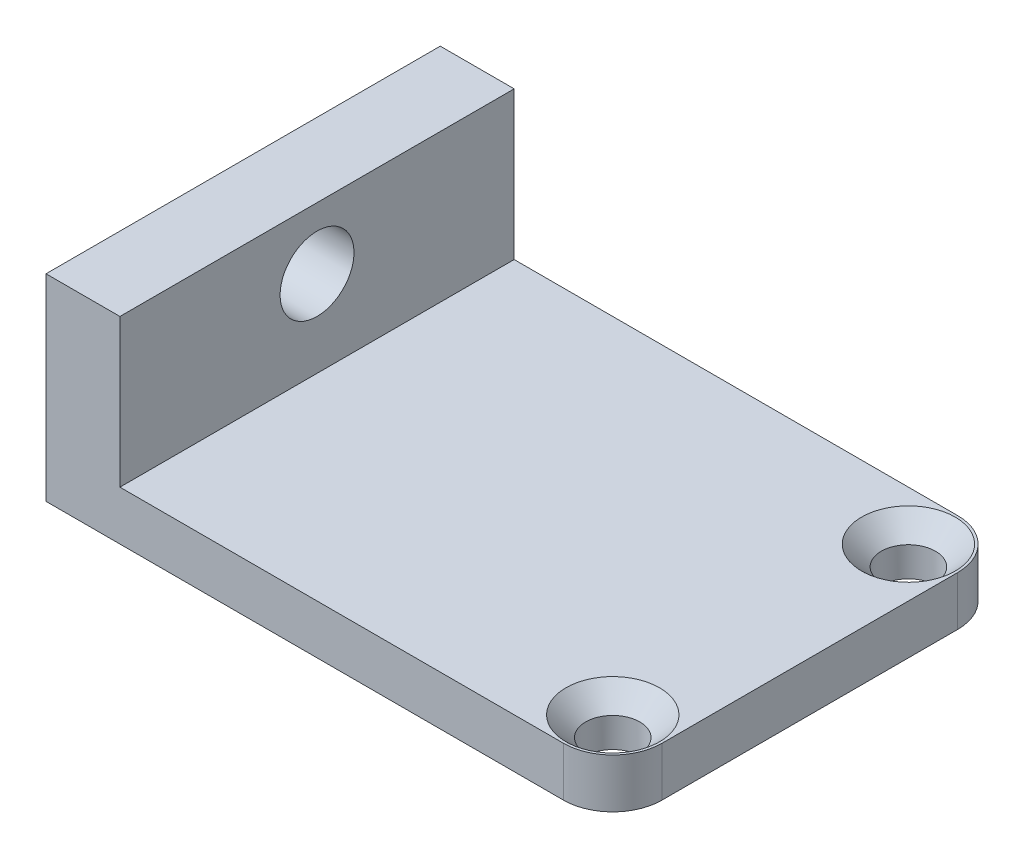
SolidWorks part; units mm, degrees
ref_plane "Front Plane" through (0, 0, 0) normal (0, 0, 1) x (1, 0, 0)
ref_plane "Top Plane" through (0, 0, 0) normal (0, 1, 0) x (1, 0, 0)
ref_plane "Right Plane" through (0, 0, 0) normal (1, 0, 0) x (0, 0, -1)
sketch "Sketch1" plane through (0, 0, 0) normal (0, 0, 1) x (1, 0, 0)
  line L0 (0, 0) -> (0, 8)
  line L1 (0, 8) -> (3, 8)
  line L2 (3, 8) -> (3, 2)
  line L3 (3, 2) -> (23, 2)
  line L4 (23, 2) -> (23, 0)
  line L5 (23, 0) -> (0, 0)
  dimension "D1" = 20
  dimension "D2" = 2
  dimension "D3" = 3
  dimension "D4" = 8
extrude "Boss-Extrude1" add sketch "Sketch1" along normal blind 16
sketch "Sketch2" plane through (0, 2, 0) normal (0, 1, 0) x (1, 0, 0)
  line L0 (23, 0) -> (3, 0) construction
  line L1 (3, -16) -> (3, 0) construction
  circle A0 centre (21, -2) radius 1.1
  circle A1 centre (21, -14) radius 1.1
  dimension "D1" = 2.2
  dimension "D2" = 2.2
  dimension "D3" = 2
  dimension "D4" = 12
  dimension "D5" = 18
  dimension "D6" = 18
extrude "Cut-Extrude1" cut sketch "Sketch2" against normal blind 2
sketch "Sketch3" plane through (0, 0, 0) normal (-1, 0, 0) x (0, 0, 1)
  line L0 (16, 0) -> (0, 0) construction
  line L1 (0, 8) -> (0, 0) construction
  circle A0 centre (8, 5.5) radius 1.5
  dimension "D3" = 3
  dimension "D1" = 5.5
  dimension "D2" = 8
extrude "Cut-Extrude2" cut sketch "Sketch3" against normal through all
chamfer "Chamfer1" distance 0.8 angle 45 2 edges at (21, 2, 15.1) (21, 2, 3.1)
fillet "Fillet1" radius 2 2 edges at (23, 1, 16) (23, 1, 0)
